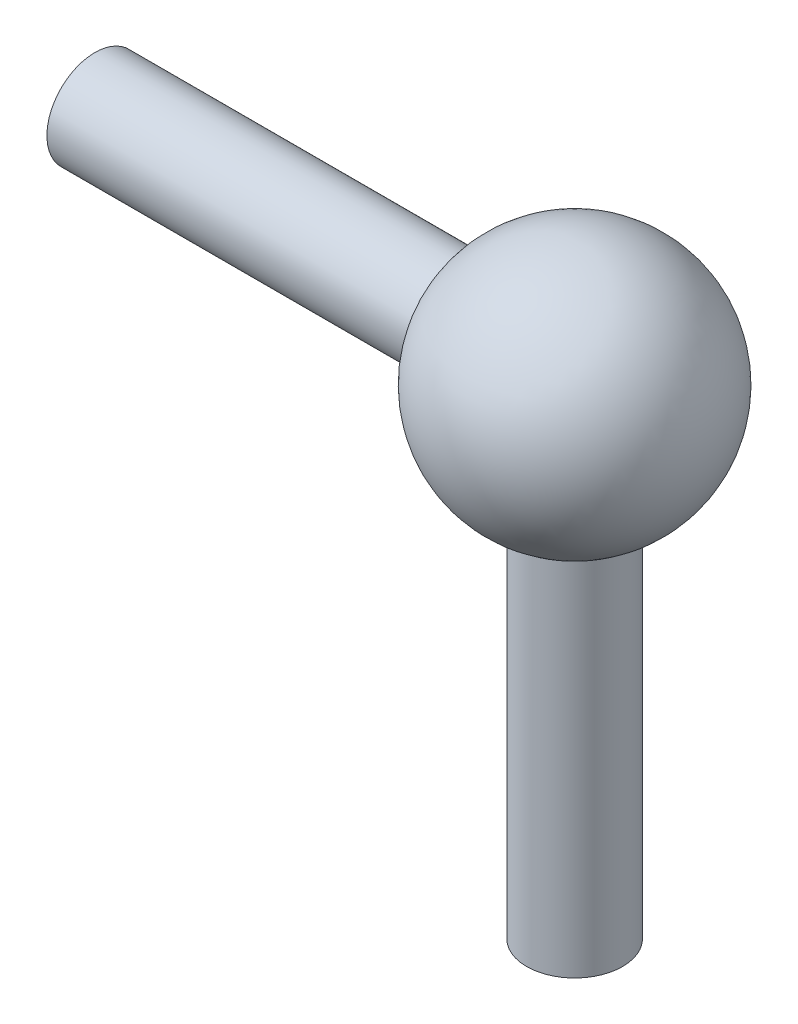
SolidWorks part; units mm, degrees
ref_plane "정면" through (0, 0, 0) normal (0, 0, 1) x (1, 0, 0)
ref_plane "윗면" through (0, 0, 0) normal (0, 1, 0) x (1, 0, 0)
ref_plane "우측면" through (0, 0, 0) normal (1, 0, 0) x (0, 0, -1)
sketch "스케치1" plane through (0, 0, 0) normal (0, 0, 1) x (1, 0, 0)
  line L0 (0, 7.6428) -> (0, -7.5287) construction
  line L1 (0, -6.5) -> (0, 6.5)
  arc A0 (0, 6.5) -> (0, -6.5) centre (0, 0) ccw
  dimension "D1" = 6.5
revolve "회전1" add sketch "스케치1" angle 360 about L0
ref_plane "평면1" through (0, -25, 0) normal (0, -1, 0) x (-1, 0, 0)
ref_plane "평면2" through (-25, 0, 0) normal (1, 0, 0) x (0, 0, -1)
sketch "스케치3" plane through (0, 0, 0) normal (1, 0, 0) x (0, 0, -1)
  circle A0 centre (0, 0) radius 2.5
  dimension "D1" = 5
extrude "보스-돌출2" add sketch "스케치3" against normal up to surface (25 mm away) up to plane "평면2"
sketch "스케치2" plane through (0, 0, 0) normal (0, 1, 0) x (1, 0, 0)
  circle A0 centre (0, 0) radius 2.5
  dimension "D1" = 5
extrude "보스-돌출1" add sketch "스케치2" against normal up to surface (25 mm away) up to plane "평면1"
